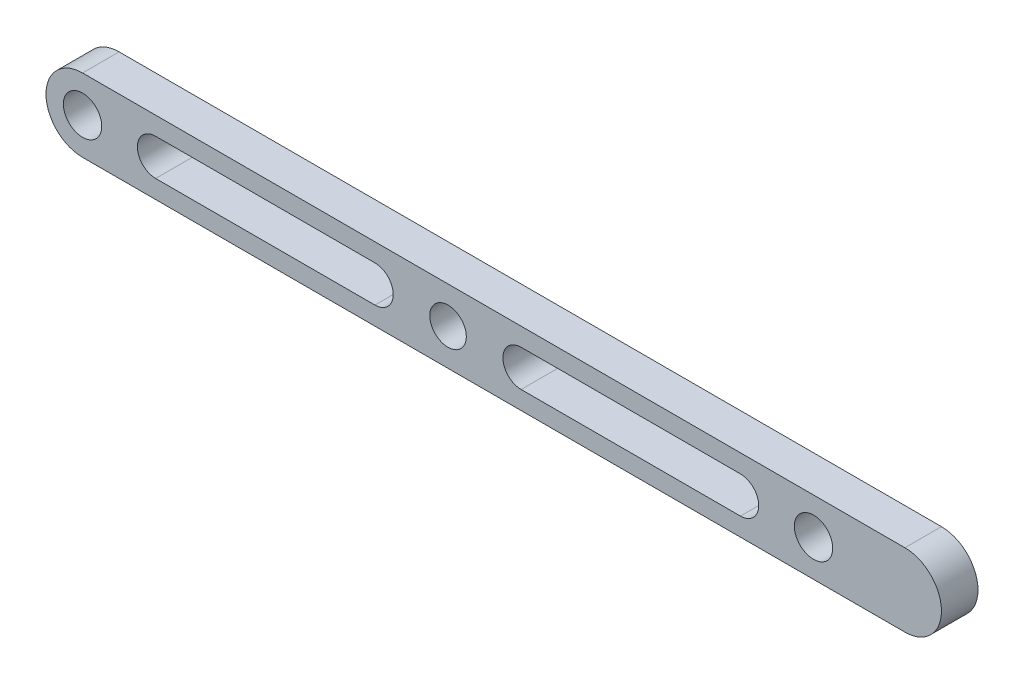
SolidWorks part; units mm, degrees
ref_plane "Front" through (0, 0, 0) normal (0, 0, 1) x (1, 0, 0)
ref_plane "Top" through (0, 0, 0) normal (0, 1, 0) x (1, 0, 0)
ref_plane "Right" through (0, 0, 0) normal (1, 0, 0) x (0, 0, -1)
sketch "草图1" plane through (0, 0, 0) normal (0, 0, 1) x (1, 0, 0)
  line L0 (100, 0) -> (125, 0) construction
  line L1 (-100, 10) -> (100, 10)
  line L3 (-100, -10) -> (100, -10)
  line L4 (100, 10) -> (125, 10)
  line L5 (100, -10) -> (125, -10)
  arc A0 (-100, 10) -> (-100, -10) centre (-100, 0) ccw
  circle A1 centre (-100, 0) radius 5.25
  circle A3 centre (100, 0) radius 5.25
  arc A4 (125, -10) -> (125, 10) centre (125, 0) ccw
  point P0 (0, 0)
  point P13 (112.5, 0)
  dimension "D3" = 10.5
  dimension "D4" = 10.5
  dimension "D5" = 10
  dimension "D1" = 200
  dimension "D2" = 20
extrude "凸台-拉伸1" add sketch "草图1" along normal blind 10
sketch "草图2" plane through (0, 0, 10) normal (0, 0, 1) x (1, 0, 0)
  circle A0 centre (0, 0) radius 5
  dimension "D1" = 10
extrude "切除-拉伸1" cut sketch "草图2" against normal blind 10
sketch "草图4" plane through (0, 0, 10) normal (0, 0, 1) x (1, 0, 0)
  line L0 (-80, 0) -> (-20, 0) construction
  line L1 (20, 0) -> (80, 0) construction
  line L2 (-80, 5) -> (-20, 5)
  line L3 (-80, -5) -> (-20, -5)
  line L4 (20, 5) -> (80, 5)
  line L5 (20, -5) -> (80, -5)
  arc A0 (-80, 5) -> (-80, -5) centre (-80, 0) ccw
  arc A1 (-20, -5) -> (-20, 5) centre (-20, 0) ccw
  arc A2 (-100, 10) -> (-100, -10) centre (-100, 0) ccw construction
  arc A3 (20, 5) -> (20, -5) centre (20, 0) ccw
  arc A4 (80, -5) -> (80, 5) centre (80, 0) ccw
  circle A5 centre (100, 0) radius 5.25 construction
  point P5 (-50, 0)
  point P13 (50, 0)
  dimension "D1" = 5
  dimension "D4" = 5
  dimension "D2" = 20
  dimension "D3" = 20
  dimension "D5" = 20
  dimension "D6" = 20
extrude "切除-拉伸2" cut sketch "草图4" against normal blind 10
